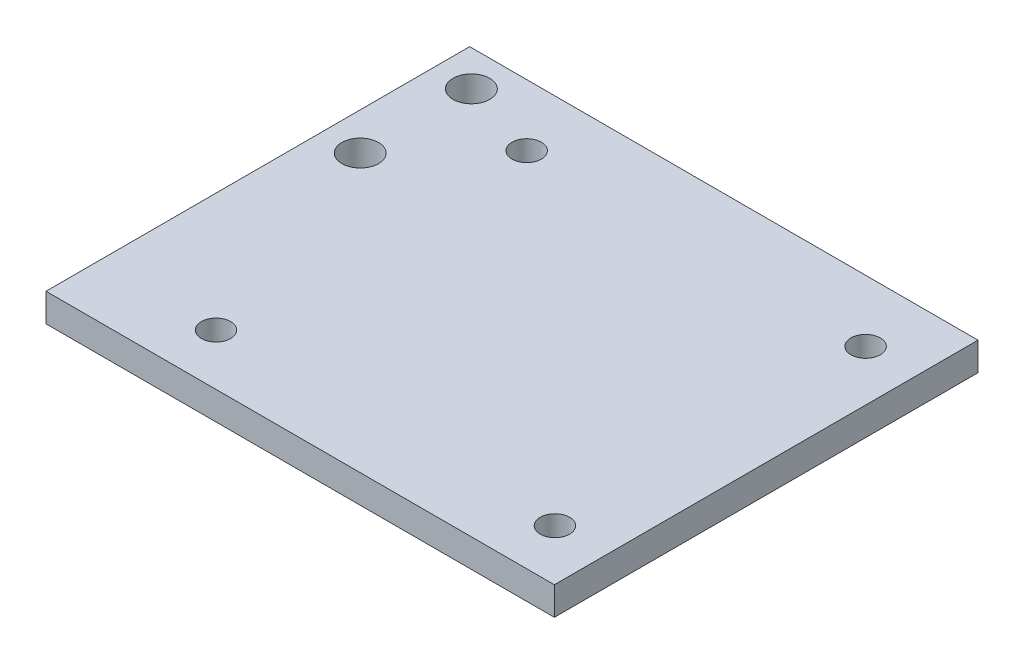
SolidWorks part; units mm, degrees
ref_plane "Front Plane" through (0, 0, 0) normal (0, 0, 1) x (1, 0, 0)
ref_plane "Top Plane" through (0, 0, 0) normal (0, 1, 0) x (1, 0, 0)
ref_plane "Right Plane" through (0, 0, 0) normal (1, 0, 0) x (0, 0, -1)
sketch "Sketch4" plane through (0, 0, 0) normal (0, 1, 0) x (1, 0, 0)
  line L1 (0, 0) -> (45.72, 0)
  line L2 (0, 0) -> (0, 38.1)
  line L3 (0, 38.1) -> (45.72, 38.1)
  line L4 (45.72, 0) -> (45.72, 38.1)
  dimension "D1" = 38.1
  dimension "D2" = 45.72
extrude "Boss-Extrude1" add sketch "Sketch4" along normal blind 2.54
sketch "Sketch5" plane through (0, 0, 0) normal (0, -1, 0) x (1, 0, 0)
  line L0 (0, -38.1) -> (0, -20.701) construction
  line L1 (0, -38.1) -> (0, 0) construction
  line L2 (0, -20.701) -> (6.731, -20.701) construction
  line L3 (6.731, -20.701) -> (6.731, -38.1) construction
  line L4 (45.72, -38.1) -> (0, -38.1) construction
  line L5 (44.069, -2.4638) -> (8.509, -2.4638) construction
  line L7 (8.509, -2.4638) -> (8.509, -35.56) construction
  line L8 (8.509, -35.56) -> (44.069, -35.56) construction
  line L10 (44.069, -35.56) -> (44.069, -2.4638) construction
  circle A0 centre (3.3655, -24.892) radius 1.65
  circle A1 centre (3.3655, -34.892) radius 1.65
  circle A2 centre (10.668, -4.6228) radius 1.32
  circle A3 centre (10.668, -32.5628) radius 1.32
  circle A4 centre (41.148, -4.6228) radius 1.32
  circle A5 centre (41.148, -32.5628) radius 1.32
  point P25 (0, 0)
  point P26 (0, 0)
  point P27 (0, 0)
  point P28 (0, 0)
  point P29 (0, 0)
  point P30 (0, 0)
  dimension "D3" = 3.3
  dimension "D11" = 2.64
  dimension "D1" = 6.731
  dimension "D2" = 17.399
  dimension "D4" = 3.3655
  dimension "D5" = 10
  dimension "D6" = 4.191
  dimension "D7" = 33.0962
  dimension "D8" = 35.56
  dimension "D9" = 2.54
  dimension "D10" = 1.778
  dimension "D12" = 2.159
  dimension "D13" = 2.159
  dimension "D14" = 27.94
  dimension "D15" = 30.48
extrude "Cut-Extrude1" cut sketch "Sketch5" against normal up to surface (2.54 mm away) up to face at (22.86, 2.54, -19.05)
